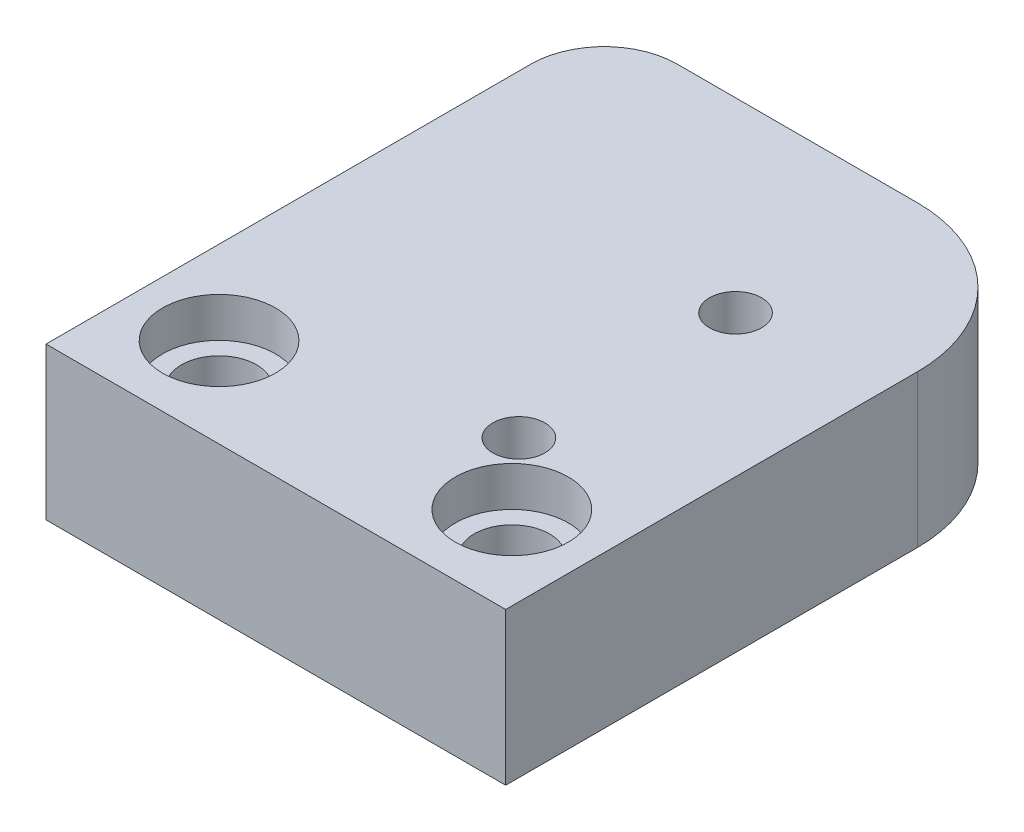
SolidWorks part; units mm, degrees
material "Acrylic (Blue)"
ref_plane "Front Plane" through (0, 0, 0) normal (0, 0, 1) x (1, 0, 0)
ref_plane "Top Plane" through (0, 0, 0) normal (0, 1, 0) x (1, 0, 0)
ref_plane "Right Plane" through (0, 0, 0) normal (1, 0, 0) x (0, 0, -1)
sketch "Sketch1" plane through (0, 0, 0) normal (0, 1, 0) x (1, 0, 0)
  line L1 (-9.9695, 24.2062) -> (9.9695, 24.2062)
  line L2 (-9.9695, 24.2062) -> (-9.9695, 0)
  line L3 (-9.9695, 0) -> (9.9695, 0)
  line L4 (9.9695, 24.2062) -> (9.9695, 0)
  dimension "D1" = 24.2062
  dimension "D2" = 19.939
extrude "Boss-Extrude1" add sketch "Sketch1" along normal blind 6.604
hole_wizard "#4-40 Tapped Hole1" positions "Sketch8" profile "Sketch9" tap size "#4-40" standard "ANSI Inch" end condition up to next
sketch "Sketch8" plane through (0, 6.604, 0) normal (0, 1, 0) x (1, 0, 0)
  line L0 (0, 0) -> (0, 11.43) construction
  line L1 (-9.9695, 0) -> (9.9695, 0) construction
  line L2 (0, 11.43) -> (3.81, 11.43) construction
  line L4 (3.81, 16.129) -> (3.81, 6.731) construction
  point P8 (3.81, 16.129)
  point P9 (3.81, 6.731)
  dimension "D1" = 9.398
  dimension "D2" = 3.81
  dimension "D3" = 11.43
sketch "Sketch9" plane through (3.81, 6.604, -16.129) normal (1, 0, 0) x (0, 0, 1)
  line L0 (0, 0) -> (0, 6.604)
  line L1 (0, 6.604) -> (1.1303, 6.604)
  line L2 (1.1303, 6.604) -> (1.1303, 0)
  line L5 (1.1303, 0) -> (0, 0)
  line L11 (0, -6.35) -> (0, 107.95) construction
  dimension "Thread Major Dia." = 2.2606
  dimension "Thru Tap Drill Depth" = 6.604
hole_wizard "CBORE for #4 Binding Head Machine Screw2" positions "Sketch3" profile "Sketch2" counterbore size "#4" standard "ANSI Inch" end condition through all
sketch "Sketch3" plane through (0, 6.604, 0) normal (0, 1, 0) x (1, 0, 0)
  line L7 (0, 0) -> (0, 3.8862) construction
  line L9 (-6.35, 3.8862) -> (6.35, 3.8862) construction
  point P43 (-6.35, 3.8862)
  point P45 (6.35, 3.8862)
  dimension "D1" = 12.7
  dimension "D2" = 3.8862
sketch "Sketch2" plane through (-6.35, 6.604, -3.8862) normal (1, 0, 0) x (0, 0, 1)
  line L0 (0, 0) -> (0, 6.604)
  line L1 (0, 6.604) -> (1.6319, 6.604)
  line L3 (1.6319, 6.604) -> (1.6319, 1.7272)
  line L4 (1.6319, 1.7272) -> (2.4511, 1.7272)
  line L5 (2.4511, 1.7272) -> (2.4511, 0)
  line L7 (2.4511, 0) -> (0, 0)
  line L11 (0, -6.35) -> (0, 107.95) construction
  dimension "Thru Hole Dia." = 3.2639
  dimension "Thru Hole Depth" = 6.604
  dimension "C'Bore Dia." = 4.9022
  dimension "C'Bore Depth" = 1.7272
fillet "Fillet1" radius 6.35 1 edges at (9.9695, 3.302, -24.2062)
fillet "Fillet2" radius 3.175 1 edges at (-9.9695, 3.302, -24.2062)
other "Move Face1" [suppressed] parameters "D1"=0.0508
